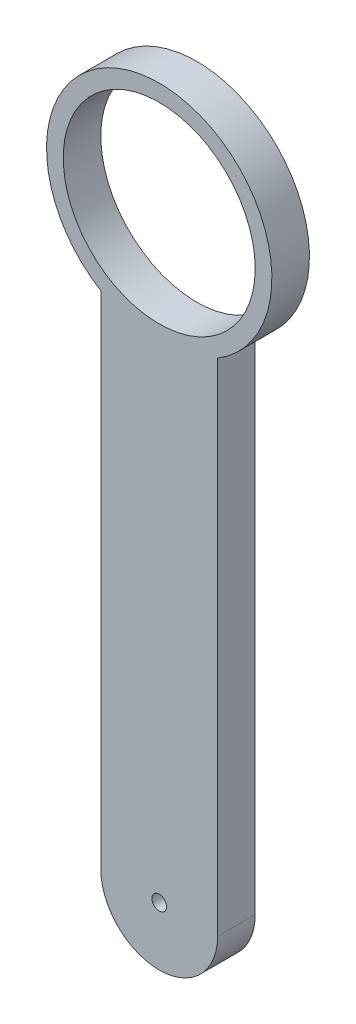
SolidWorks part; units mm, degrees
ref_plane "前视基准面" through (0, 0, 0) normal (0, 0, 1) x (1, 0, 0)
ref_plane "上视基准面" through (0, 0, 0) normal (0, 1, 0) x (1, 0, 0)
ref_plane "右视基准面" through (0, 0, 0) normal (1, 0, 0) x (0, 0, -1)
sketch "草图4" plane through (0, 0, 0) normal (0, 0, 1) x (1, 0, 0)
  line L2 (0, 0) -> (0, 120)
  line L4 (28, 0) -> (28, 120)
  arc A0 (0, 0) -> (28, 0) centre (14, 0) ccw
  arc A1 (28, 120) -> (0, 120) centre (14, 143.0868) ccw
  circle A2 centre (14, 143.0868) radius 23
  dimension "D3" = 27
  dimension "D1" = 28
  dimension "D2" = 120
extrude "凸台-拉伸2" add sketch "草图4" along normal blind 9 contours A0 L4 A1 L2 | A2
sketch "草图5" plane through (0, 0, 0) normal (0, 0, -1) x (-1, 0, 0)
  circle A0 centre (-14, 0) radius 1.75
extrude "切除-拉伸1" cut sketch "草图5" against normal blind 10
